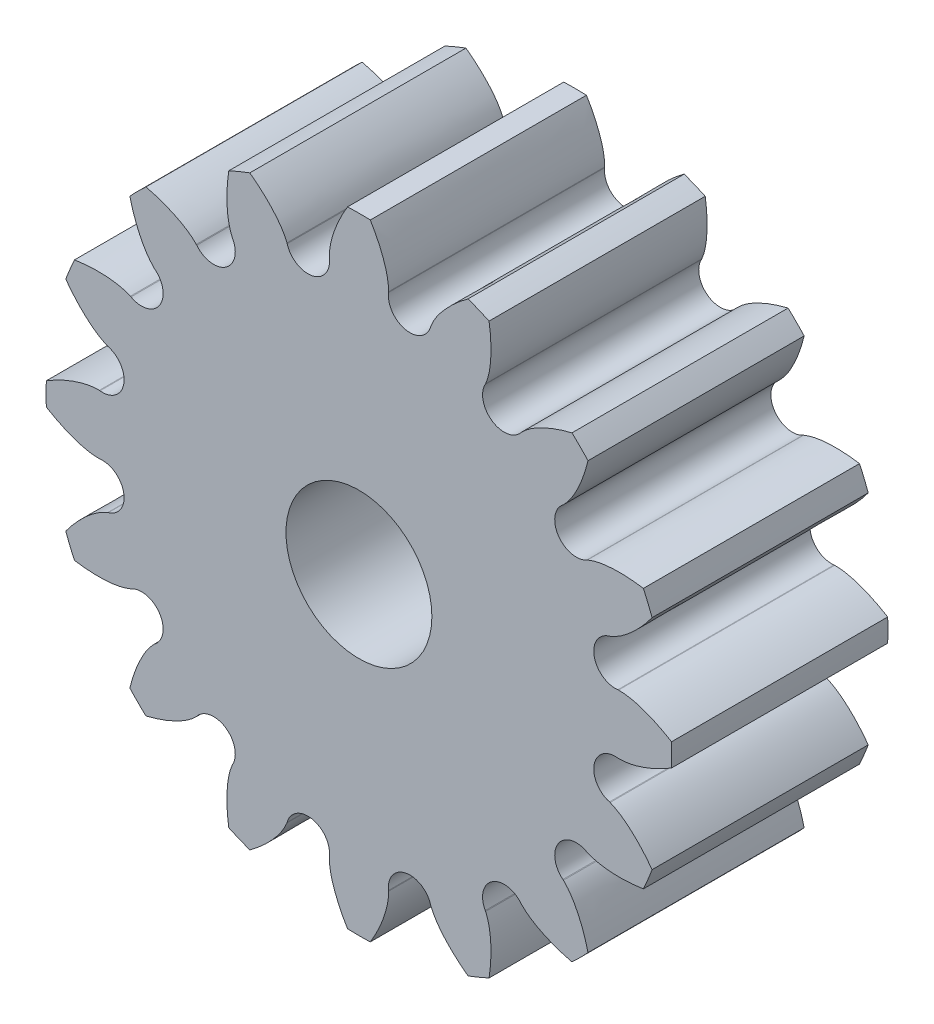
SolidWorks part; units mm, degrees
material "PE Low/Medium Density"
ref_plane "Front Plane" through (0, 0, 0) normal (0, 0, 1) x (1, 0, 0)
ref_plane "Top Plane" through (0, 0, 0) normal (0, 1, 0) x (1, 0, 0)
ref_plane "Right Plane" through (0, 0, 0) normal (1, 0, 0) x (0, 0, -1)
sketch "Involute construction sketch" plane through (0, 0, 0) normal (0, 0, 1) x (1, 0, 0)
  line L0 (0, 0) -> (-1.7946, 3.1652) construction
  line L1 (0, 0) -> (-1.096, 3.4696) construction
  line L2 (0, 0) -> (-0.3494, 3.6218) construction
  line L3 (0, 0) -> (0.4126, 3.6151) construction
  line L4 (-2.9284, 2.1595) -> (-2.4145, 2.722) construction
  line L5 (-2.4145, 2.722) -> (-1.7946, 3.1652) construction
  line L6 (-1.7946, 3.1652) -> (-1.096, 3.4696) construction
  line L7 (0, 0) -> (-2.4145, 2.722) construction
  line L8 (0, 0) -> (-2.9284, 2.1595) construction
  line L9 (-1.096, 3.4696) -> (-0.3494, 3.6218) construction
  line L10 (-0.3494, 3.6218) -> (0.4126, 3.6151) construction
  line L11 (-2.9284, 2.1595) -> (-0.6672, 5.2259) construction
  line L12 (-2.4145, 2.722) -> (-0.1342, 4.7446) construction
  line L13 (-1.7946, 3.1652) -> (0.194, 4.2927) construction
  line L14 (-1.096, 3.4696) -> (0.3572, 3.9286) construction
  line L15 (-0.3494, 3.6218) -> (0.4091, 3.6949) construction
  line L17 (0, 0) -> (0, 5.7859) construction
  line L18 (0, 0) -> (0.3795, 3.8534) construction
  line L19 (0, 0) -> (0.6516, 3.2759) construction
  circle A0 centre (0, 0) radius 3.3401 construction
  circle A1 centre (0, 0) radius 3.6386 construction
  circle A2 centre (0, 0) radius 3.8721 construction
  circle A3 centre (0, 0) radius 4.3561 construction
  spline S0 degree 3 poles (0.4126, 3.6151) (0.4138, 3.7219) (0.3608, 3.9584) (0.0805, 4.5656) (-0.328, 4.974) (-0.6672, 5.2259) knots 0 0 0 0 0.160058 0.360049 1 1 1 1 construction
  point P17 (0.1584, 4.3532)
  dimension "D1" = 6.6802
  dimension "D2" = 7.2771
  dimension "D3" = 7.7442
  dimension "D4" = 8.7122
  dimension "D5" = 0.762
  dimension "D6" = 1.524
  dimension "D7" = 2.286
  dimension "D8" = 3.048
  dimension "D9" = 3.81
  dimension "D10" = 5.625
  dimension "D11" = 11.25
sketch "Sketch2" plane through (0, 0, 0) normal (0, 0, 1) x (1, 0, 0)
  line L0 (0, 4.3561) -> (0, 3.3401)
  line L1 (0, 0) -> (0, 5.7859) construction
  line L2 (0.4126, 3.6151) -> (0.4114, 3.605)
  line L3 (0, 0) -> (0.4126, 3.6151) construction
  circle A0 centre (0, 0) radius 4.3561 construction
  circle A1 centre (0, 0) radius 3.3401 construction
  arc A2 (0, 4.3561) -> (0.1584, 4.3532) centre (0, 0) cw
  arc A3 (0, 3.3401) -> (0.6516, 3.2759) centre (0, 0) cw
  arc A4 (0.4114, 3.605) -> (0.6516, 3.2759) centre (0.7103, 3.5709) ccw
  spline S0 degree 3 poles (0.1584, 4.3532) (0.2397, 4.2197) (0.3556, 3.9815) (0.4138, 3.7219) (0.4126, 3.6151) knots 0 0 0 0 0.595051 1 1 1 1
sketch "Sketch3" plane through (0, 0, 0) normal (0, 0, 1) x (1, 0, 0)
  circle A0 centre (0, 0) radius 3.3401
  circle A1 centre (0, 0) radius 1.016
  dimension "D1" = 6.6802
  dimension "D2" = 2.032
extrude "Base" add sketch "Sketch3" along normal blind 3.0099
extrude "Half tooth" add sketch "Sketch2" along normal up to surface (3.0099 mm away) up to face at (3.3401, 0, 3.0099)
ref_plane "Midplane of half tooth" through (0, 0, 0) normal (-1, 0, 0) x (0, 0, 1)
mirror "Mirror of half tooth" about plane through (0, 0, 0) normal (-1, 0, 0) of "Half tooth"
pattern_circular "Pattern of tooth" count 16 over 360 about axis through (0, 0, 3.0099) along (0, 0, 1) of "Half tooth", "Mirror of half tooth"
equation "\"radtodeg\"= 180 / PI'radian to degree conversion [ ]"
equation "\"phi\"= 20'pressure angle [deg]"
equation "\"N\"= 16'number of teeth [teeth]"
equation "\"A\"= 0.343in'diameter of addendum circle [inch]"
equation "\"B\"= 0.263in'diameter of dedendum circle [inch]"
equation "\"P\"= ( \"N\" + 2 ) / \"A\"'diametral pitch [teeth/inch]"
equation "\"d\"= \"N\" / \"P\"'diameter of pitch circle [inch]"
equation "\"cp\"= PI / \"P\"'circular pitch [inch/teeth]"
equation "\"add\"= 1 / \"P\"'addendum [inch]"
equation "\"ded\"= - ( \"B\" - \"d\" ) / 2'dedendum [inch]"
equation "\"clear\"= \"ded\" - \"add\"'clearance [inch]"
equation "\"C\"= \"B\" + 2 * \"clear\"'diameter of clearance circle [inch]"
equation "\"h\"= \"add\" + \"ded\"'tooth height / whole depth [inch]"
equation "\"s\"= \"d\" * cos ( \"phi\" * 1 / \"radtodeg\" )'diameter of base circle [inch]"
equation "\"t\"= ( PI / 2 ) / \"P\"'tooth width at diameter of pitch circle diameter [inch]"
equation "\"alpha\"= ( \"t\" / ( \"d\" / 2 ) * \"radtodeg\" ) / 2'arc angle for half of tooth width at pitch circle diameter [inch]"
equation "\"bore\"= 0.0800'bore of hub [inch]"
equation "\"D4@Involute construction sketch\"= \"A\"'addendum circle"
equation "\"D3@Involute construction sketch\"= \"d\"'pitch circle"
equation "\"D2@Involute construction sketch\"= \"s\"'base circle"
equation "\"D1@Involute construction sketch\"= \"B\"'dedendum circle"
equation "\"seg\"= \"D5@Involute construction sketch\"'size of one involute segment [inch]"
equation "\"D6@Involute construction sketch\"=2*\"seg\""
equation "\"D7@Involute construction sketch\"=3*\"seg\""
equation "\"D8@Involute construction sketch\"=4*\"seg\""
equation "\"D9@Involute construction sketch\"=5*\"seg\""
equation "\"D10@Involute construction sketch\"=\"alpha\""
equation "\"D11@Involute construction sketch\"=2*\"alpha\""
equation "\"D1@Sketch3\"=\"B\""
equation "\"D1@CirPattern1\"=\"N\""
equation "\"D2@Sketch3\"=\"bore\""
equation "\"D1@Pattern of tooth\"=\"N\""
